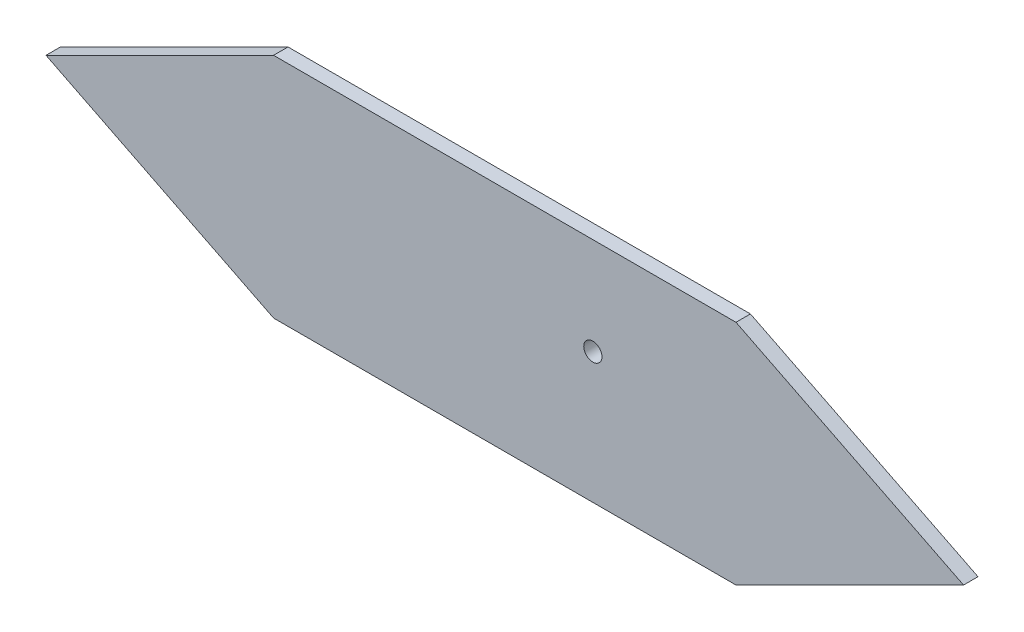
SolidWorks part; units mm, degrees
material "AISI 316 Annealed Stainless Steel Bar (SS)"
ref_plane "Front Plane" through (0, 0, 0) normal (0, 0, 1) x (1, 0, 0)
ref_plane "Top Plane" through (0, 0, 0) normal (0, 1, 0) x (1, 0, 0)
ref_plane "Right Plane" through (0, 0, 0) normal (1, 0, 0) x (0, 0, -1)
sketch "Sketch1" plane through (0, 0, 0) normal (0, 0, 1) x (1, 0, 0)
  line L0 (0, 50) -> (-100, 50) construction
  line L1 (0, 0) -> (203.2, 0)
  line L2 (0, 0) -> (0, 100)
  line L3 (0, 100) -> (203.2, 100)
  line L4 (203.2, 0) -> (203.2, 100)
  line L5 (101.6, 0) -> (101.6, 100) construction
  line L6 (0, 100) -> (-100, 50)
  line L7 (-100, 50) -> (0, 0)
  line L8 (303.2, 50) -> (203.2, 0)
  line L9 (203.2, 100) -> (303.2, 50)
  dimension "D3" = 100
  dimension "D1" = 203.2
  dimension "D2" = 100
extrude "Boss-Extrude1" add sketch "Sketch1" along normal blind 6.35
sketch "Sketch2" plane through (0, 0, 0) normal (0, 0, -1) x (-1, 0, 0)
  line L0 (0, 0) -> (-203.2, 0) construction
  line L5 (-203.2, 6.7) -> (-177.8, 6.7)
  line L6 (-203.2, 6.7) -> (-203.2, 12.7)
  line L7 (-203.2, 12.7) -> (-177.8, 12.7)
  line L8 (-177.8, 6.7) -> (-177.8, 12.7)
  line L9 (6, 25.05) -> (6, 6.7)
  line L10 (-101.6, 0) -> (-101.6, 100) construction
  line L11 (0, 100) -> (-203.2, 100) construction
  line L20 (0, 6.7) -> (6, 6.7)
  line L21 (-203.2, 19.05) -> (-177.8, 19.05)
  line L22 (-203.2, 19.05) -> (-203.2, 25.05)
  line L23 (-203.2, 25.05) -> (-177.8, 25.05)
  line L24 (-177.8, 19.05) -> (-177.8, 25.05)
  line L25 (-203.2, 19.05) -> (-203.2, 12.7)
  line L26 (-203.2, 25.05) -> (-209.2, 25.05)
  line L31 (-203.2, 25.05) -> (-203.2, 6.7)
  line L36 (-203.2, 6.7) -> (-209.2, 6.7)
  line L37 (-209.2, 25.05) -> (-209.2, 6.7)
  line L38 (0, 25.05) -> (0, 6.7)
  line L39 (0, 25.05) -> (6, 25.05)
  line L40 (0, 19.05) -> (0, 12.7)
  line L41 (-25.4, 19.05) -> (-25.4, 25.05)
  line L50 (0, 25.05) -> (-25.4, 25.05)
  line L51 (0, 19.05) -> (0, 25.05)
  line L52 (0, 19.05) -> (-25.4, 19.05)
  line L53 (-25.4, 6.7) -> (-25.4, 12.7)
  line L54 (0, 12.7) -> (-25.4, 12.7)
  line L55 (0, 6.7) -> (0, 12.7)
  line L56 (0, 6.7) -> (-25.4, 6.7)
  dimension "D1" = 25.4
  dimension "D2" = 6.35
  dimension "D3" = 12.7
  dimension "D4" = 6
  dimension "D5" = 6
  dimension "D6" = 6
  dimension "D7" = 101.6
extrude "Boss-Extrude3" add sketch "Sketch2" along normal blind 25
sketch "Sketch3" plane through (0, 0, 0) normal (0, 0, -1) x (-1, 0, 0)
  circle A0 centre (-140.3, 57.4) radius 4
  dimension "D1" = 8
  dimension "D2" = 62.9
  dimension "D3" = 38.35
extrude "Cut-Extrude1" cut sketch "Sketch3" against normal blind 25
